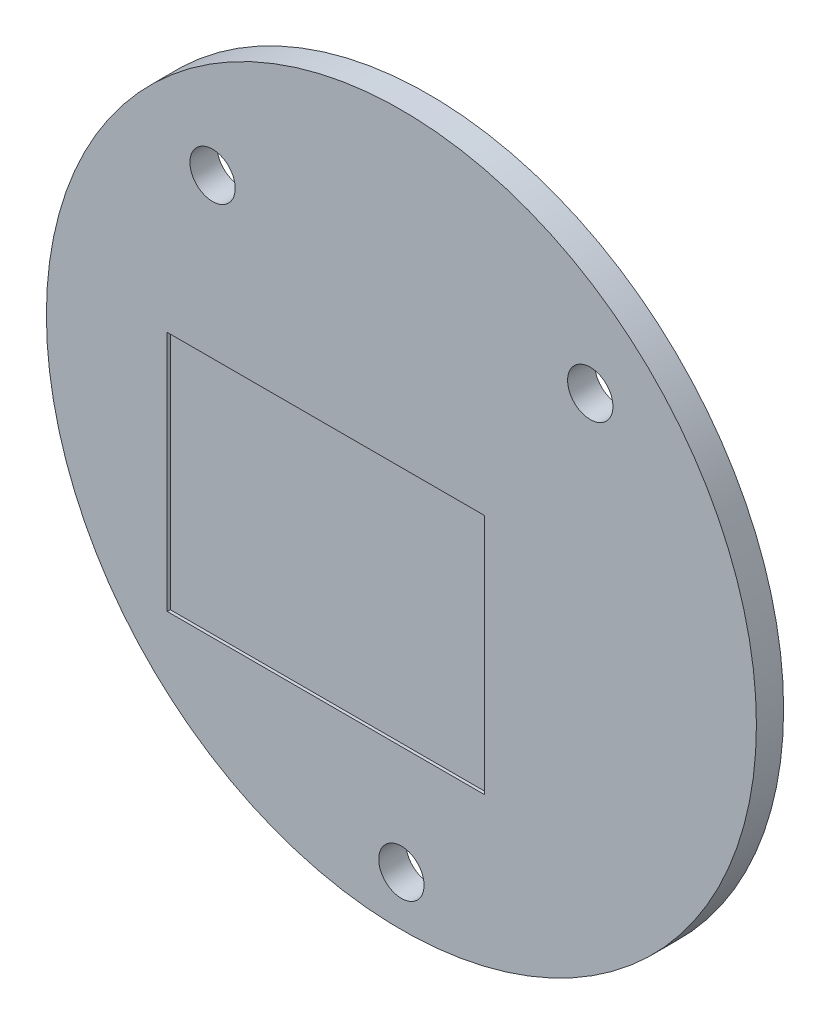
SolidWorks part; units mm, degrees
ref_plane "Alzado" through (0, 0, 0) normal (0, 0, 1) x (1, 0, 0)
ref_plane "Planta" through (0, 0, 0) normal (0, 1, 0) x (1, 0, 0)
ref_plane "Vista lateral" through (0, 0, 0) normal (1, 0, 0) x (0, 0, -1)
sketch "Croquis1" plane through (0, 0, 0) normal (0, 0, 1) x (1, 0, 0)
  line L0 (-12.5, 13.5) -> (12.5, 13.5) construction
  circle A0 centre (0, 0) radius 23.5
  circle A1 centre (0, -20.2) radius 1.5
  circle A2 centre (-12.5, 13.5) radius 1.5
  circle A3 centre (12.5, 13.5) radius 1.5
  point P5 (0, 13.5)
  dimension "D3" = 3
  dimension "D11" = 47
  dimension "D1" = 25
  dimension "D2" = 13.5
  dimension "D4" = 20.2
extrude "Saliente-Extruir1" add sketch "Croquis1" along normal blind 1.8
sketch "Croquis2" plane through (0, 0, 1.8) normal (0, 0, 1) x (1, 0, 0)
  line L0 (-14.5, -12) -> (-14.5, 2) construction
  line L1 (-14.5, -12) -> (4.5, -12) construction
  line L2 (4.5, -12) -> (4.5, 2) construction
  line L3 (-14.5, 2) -> (4.5, 2) construction
  line L4 (-3.5, -1) -> (-3.5, 1) construction
  line L5 (-3.5, -1) -> (3.5, -1) construction
  line L6 (3.5, -1) -> (3.5, 1) construction
  line L7 (-3.5, 1) -> (3.5, 1) construction
  line L8 (-3.5, -1) -> (3.5, 1) construction
  line L9 (3.5, -1) -> (-3.5, 1) construction
  line L10 (-15.5, 3) -> (5.5, 3)
  line L11 (5.5, -13) -> (5.5, 3)
  line L12 (-15.5, -13) -> (5.5, -13)
  line L13 (-15.5, -13) -> (-15.5, 3)
  dimension "D1" = 2
  dimension "D2" = 7
  dimension "D3" = 1
  dimension "D4" = 14
  dimension "D5" = 19
  dimension "D6" = 1
extrude "Cortar-Extruir1" cut sketch "Croquis2" against normal blind 0.2
